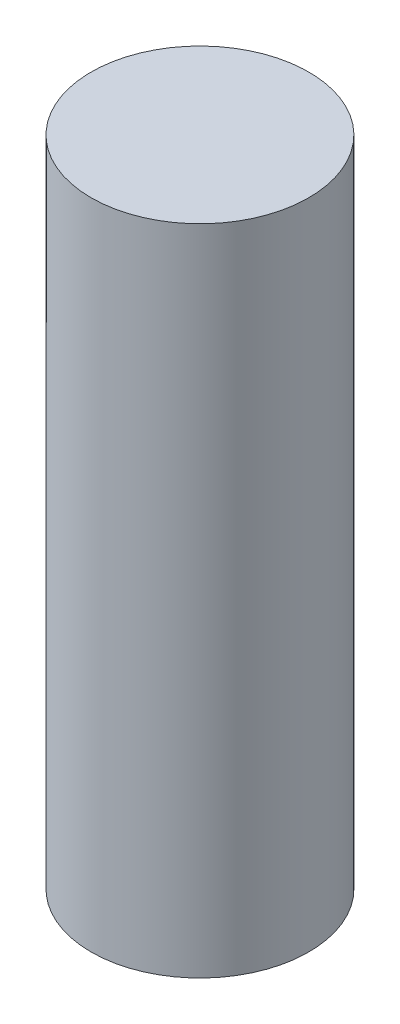
SolidWorks part; units mm, degrees
ref_plane "Front Plane" through (0, 0, 0) normal (0, 0, 1) x (1, 0, 0)
ref_plane "Top Plane" through (0, 0, 0) normal (0, 1, 0) x (1, 0, 0)
ref_plane "Right Plane" through (0, 0, 0) normal (1, 0, 0) x (0, 0, -1)
sketch "Sketch1" plane through (0, 0, 0) normal (0, 1, 0) x (1, 0, 0)
  circle A0 centre (0, 0) radius 6
  dimension "D1" = 12
extrude "Boss-Extrude1" add sketch "Sketch1" along normal blind 36
